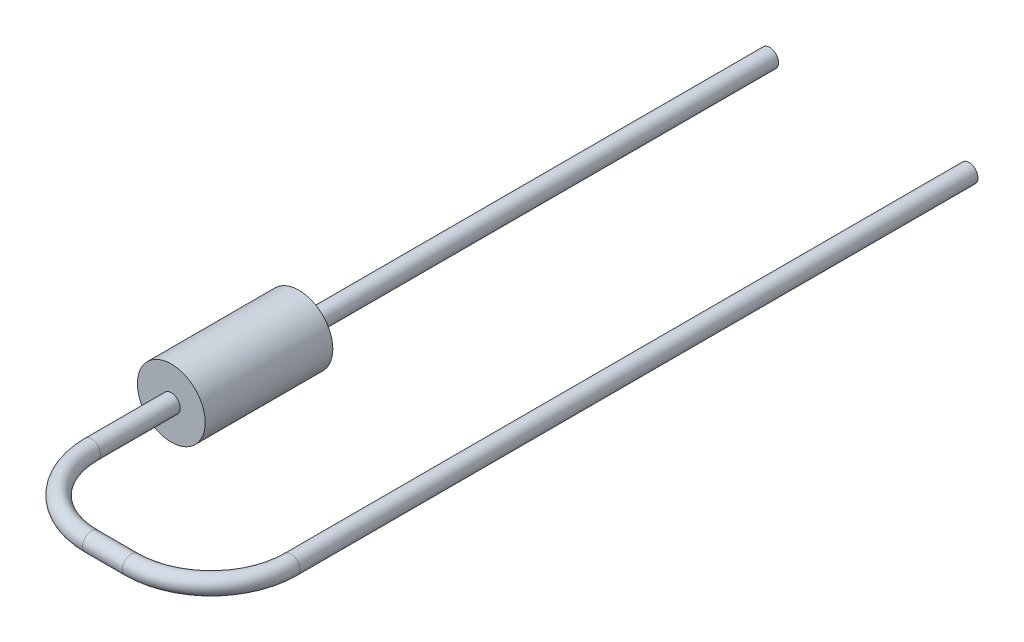
SolidWorks part; units mm, degrees
ref_plane "Front Plane" through (0, 0, 0) normal (0, 0, 1) x (1, 0, 0)
ref_plane "Top Plane" through (0, 0, 0) normal (0, 1, 0) x (1, 0, 0)
ref_plane "Right Plane" through (0, 0, 0) normal (1, 0, 0) x (0, 0, -1)
sketch "Sketch2" plane through (0, 0, 0) normal (0, 0, 1) x (1, 0, 0)
  circle A0 centre (0, 0) radius 0.85
  dimension "D1" = 1.7
extrude "Resistor Body" add sketch "Sketch2" along normal blind 3.2
sketch "Lead1 Path" plane through (0, 0, 0) normal (0, -1, 0) x (1, 0, 0)
  line L1 (0.85, 3.2) -> (-0.85, 3.2) construction
  line L2 (0, 3.2) -> (0, 0) construction
  line L3 (0, 3.2) -> (0, 5.2)
  line L4 (5, 5.2) -> (5, -11.8)
  line L5 (2, 7.2) -> (3, 7.2)
  arc A0 (2, 7.2) -> (0, 5.2) centre (2, 5.2) ccw
  arc A1 (5, 5.2) -> (3, 7.2) centre (3, 5.2) ccw
  point P11 (0, 7.2)
  point P14 (5, 7.2)
  dimension "D4" = 2
  dimension "D1" = 19
  dimension "D2" = 4
  dimension "D3" = 5
sketch "Lead1 Profile" plane through (0, 0, 3.2) normal (0, 0, 1) x (-1, 0, 0)
  circle A0 centre (0, 0) radius 0.225
  dimension "D1" = 0.45
sweep "Lead1" add profiles "Lead1 Profile" path "Lead1 Path"
sketch "Sketch6" plane through (0, 0, 0) normal (0, 0, -1) x (1, 0, 0)
  circle A0 centre (0, 0) radius 0.225 construction
  circle A1 centre (0, 0) radius 0.225
extrude "Lead2" add sketch "Sketch6" along normal up to surface (11.8 mm away) up to face at (4.775, 0, -11.8)
ref_plane "Mounting Plane" through (0, 0, -8) normal (0, 0, 1) x (1, 0, 0)
sketch "Component_Outline" plane through (0, 0, -8) normal (0, 0, 1) x (1, 0, 0)
  line L0 (5, 0.225) -> (0.8197, 0.225)
  line L1 (5, -0.225) -> (0.8197, -0.225)
  line L2 (0, -0.225) -> (2, -0.225) construction
  line L3 (2, 0.225) -> (0, 0.225) construction
  arc A0 (0.8197, 0.225) -> (0.8197, -0.225) centre (0, 0) ccw
  arc A1 (5, 0.225) -> (5, -0.225) centre (5, 0) cw
  dimension "D1" = 0.85
  dimension "D2" = 0.225
